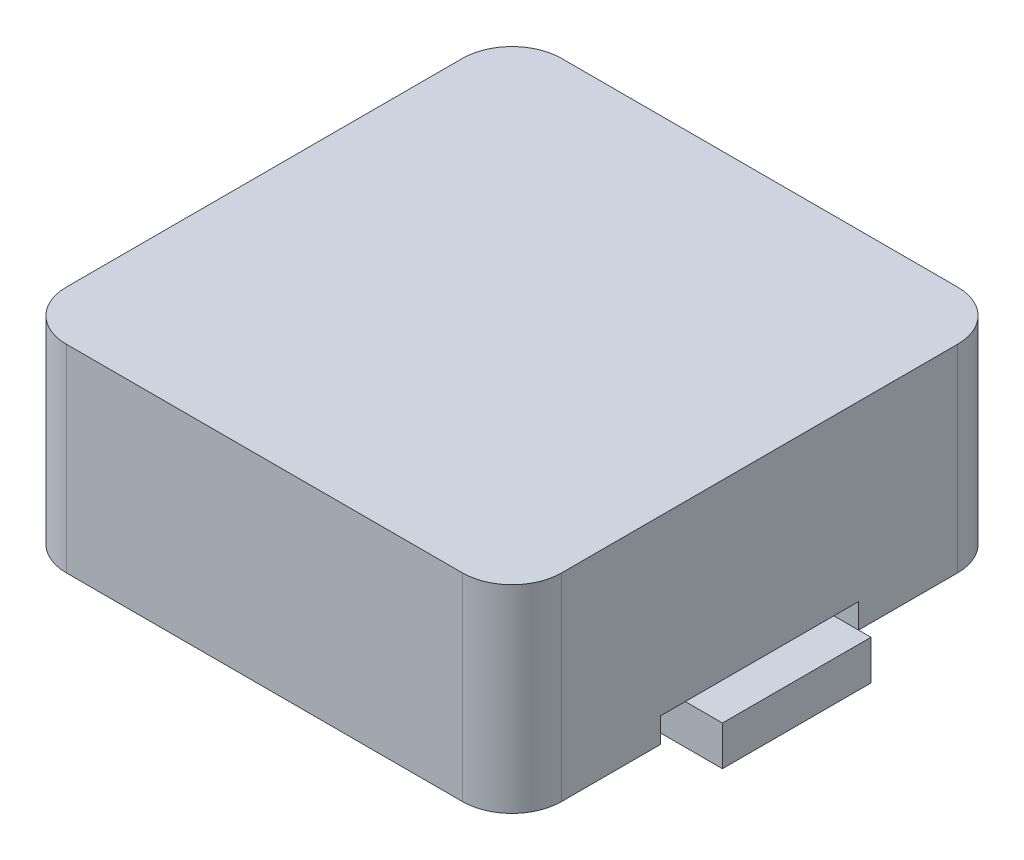
SolidWorks part; units mm, degrees
ref_plane "Front Plane" through (0, 0, 0) normal (0, 0, 1) x (1, 0, 0)
ref_plane "Top Plane" through (0, 0, 0) normal (0, 1, 0) x (1, 0, 0)
ref_plane "Right Plane" through (0, 0, 0) normal (1, 0, 0) x (0, 0, -1)
sketch "Sketch1" plane through (0, 0, 0) normal (0, 1, 0) x (1, 0, 0)
  line L1 (-4, -5) -> (4, -5)
  line L2 (-5, -4) -> (-5, 4)
  line L3 (-4, 5) -> (4, 5)
  line L4 (5, -4) -> (5, 4)
  line L5 (-5, -5) -> (5, 5) construction
  line L6 (-5, 5) -> (5, -5) construction
  arc A0 (4, 5) -> (5, 4) centre (4, 4) cw
  arc A1 (4, -5) -> (5, -4) centre (4, -4) ccw
  arc A2 (-4, -5) -> (-5, -4) centre (-4, -4) cw
  arc A3 (-5, 4) -> (-4, 5) centre (-4, 4) cw
  point P0 (0, 0)
  dimension "D1" = 1
extrude "Boss-Extrude1" add sketch "Sketch1" along normal blind 4
sketch "Sketch2" plane through (0, 0, 0) normal (0, 1, 0) x (1, 0, 0)
  line L0 (-5, 4) -> (-5, -4) construction
  line L1 (-6, -2) -> (-4, -2)
  line L2 (-6, -2) -> (-6, 2)
  line L3 (-6, 2) -> (-4, 2)
  line L4 (-4, -2) -> (-4, 2)
  line L5 (-6, -2) -> (-4, 2) construction
  line L6 (-6, 2) -> (-4, -2) construction
  line L8 (6, 2) -> (4, -2) construction
  line L9 (6, -2) -> (4, 2) construction
  line L10 (4, -2) -> (4, 2)
  line L11 (6, 2) -> (4, 2)
  line L12 (6, -2) -> (6, 2)
  line L13 (6, -2) -> (4, -2)
  point P0 (-5, 0)
  point P14 (5, 0)
extrude "Cut-Extrude1" cut sketch "Sketch2" along normal blind 0.5
sketch "Sketch3" plane through (0, 0.5, 0) normal (0, -1, 0) x (1, 0, 0)
  line L0 (-4, 1.5) -> (-4, -1.5)
  line L2 (-5.75, -1.5) -> (-4, -1.5)
  line L3 (-5.75, -1.5) -> (-5.75, 1.5)
  line L4 (-5.75, 1.5) -> (-4, 1.5)
  line L5 (5.75, -1.5) -> (5.75, 1.5)
  line L6 (-5.75, -1.5) -> (5.75, 1.5) construction
  line L7 (-5.75, 1.5) -> (5.75, -1.5) construction
  line L9 (3.9937, 1.5) -> (3.9937, -1.5)
  line L10 (3.9937, 1.5) -> (5.75, 1.5)
  line L11 (3.9937, -1.5) -> (5.75, -1.5)
  point P0 (0, 0)
  point P4 (0, 0)
extrude "Boss-Extrude2" add sketch "Sketch3" along normal blind 0.8
